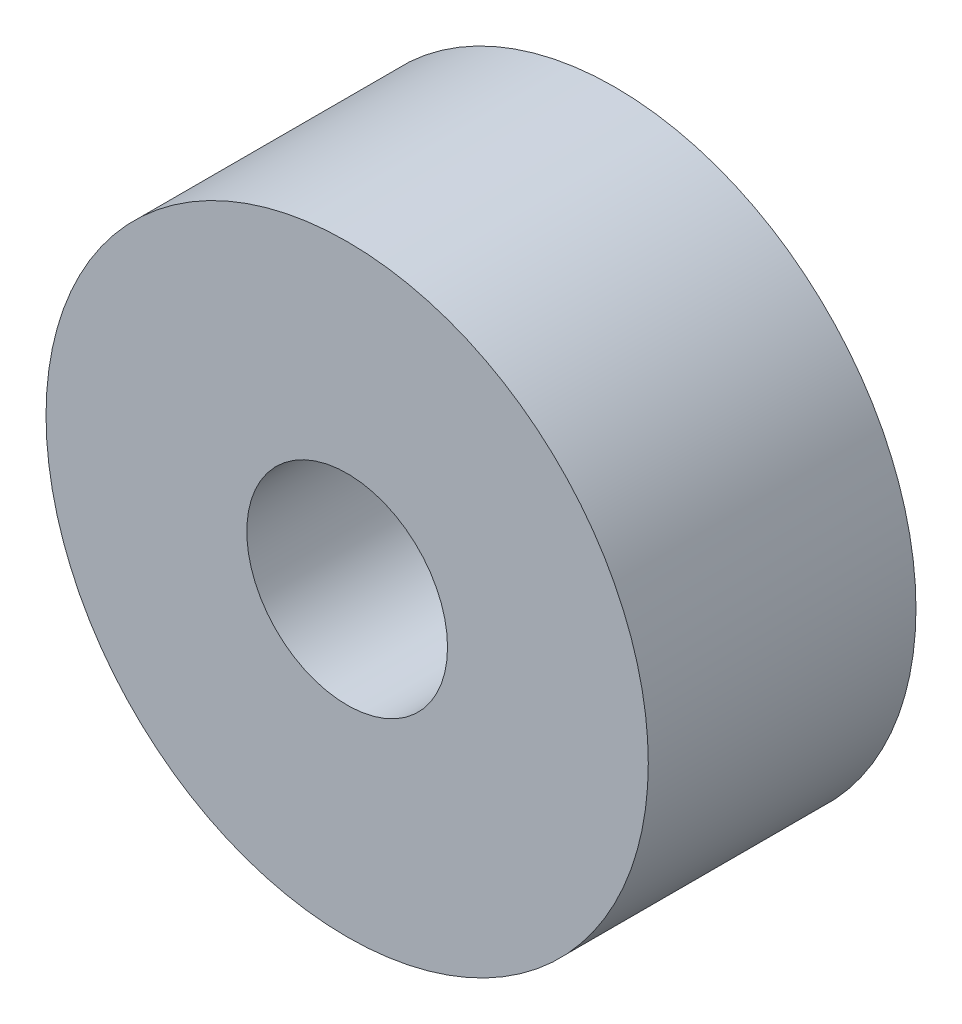
SolidWorks part; units mm, degrees
ref_plane "Plano frontal" through (0, 0, 0) normal (0, 0, 1) x (1, 0, 0)
ref_plane "Plano superior" through (0, 0, 0) normal (0, 1, 0) x (1, 0, 0)
ref_plane "Plano direito" through (0, 0, 0) normal (1, 0, 0) x (0, 0, -1)
sketch "Esboço1" plane through (0, 0, 0) normal (0, 0, 1) x (1, 0, 0)
  circle A0 centre (0, 0) radius 1.5
  circle A1 centre (0, 0) radius 4.5
  dimension "D1" = 3
  dimension "D2" = 9
extrude "Ressalto-extrusão1" add sketch "Esboço1" along normal blind 4
